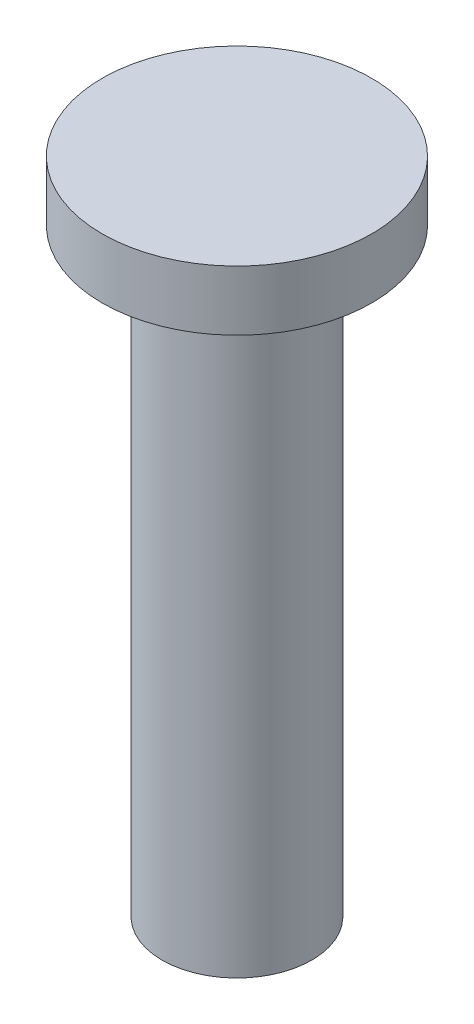
SolidWorks part; units mm, degrees
ref_plane "Front Plane" through (0, 0, 0) normal (0, 0, 1) x (1, 0, 0)
ref_plane "Top Plane" through (0, 0, 0) normal (0, 1, 0) x (1, 0, 0)
ref_plane "Right Plane" through (0, 0, 0) normal (1, 0, 0) x (0, 0, -1)
sketch "Sketch1" plane through (0, 0, 0) normal (0, 1, 0) x (1, 0, 0)
  circle A0 centre (0, 0) radius 2.5
  dimension "D1" = 5
extrude "Boss-Extrude1" add sketch "Sketch1" along normal blind 20
sketch "Sketch2" plane through (0, 20, 0) normal (0, 1, 0) x (1, 0, 0)
  circle A0 centre (0, 0) radius 4.5
  dimension "D1" = 9
extrude "Boss-Extrude2" add sketch "Sketch2" along normal blind 2
